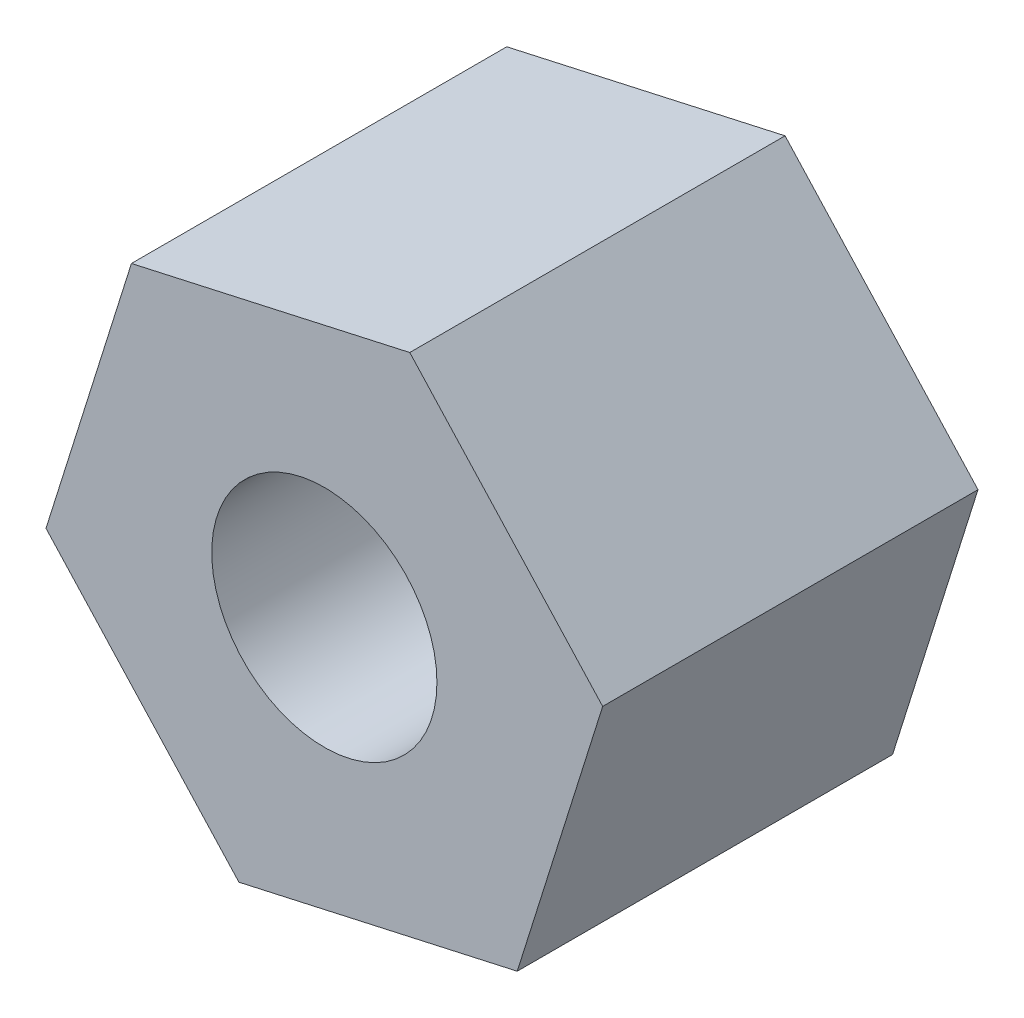
SolidWorks part; units mm, degrees
ref_plane "Front Plane" through (0, 0, 0) normal (0, 0, 1) x (1, 0, 0)
ref_plane "Top Plane" through (0, 0, 0) normal (0, 1, 0) x (1, 0, 0)
ref_plane "Right Plane" through (0, 0, 0) normal (1, 0, 0) x (0, 0, -1)
sketch "Sketch1" plane through (0, 0, 0) normal (0, 0, 1) x (1, 0, 0)
  line L1 (1.1381, 3.6245) -> (-2.5699, 2.7978)
  line L2 (-2.5699, 2.7978) -> (-3.7079, -0.8267)
  line L3 (-3.7079, -0.8267) -> (-1.1381, -3.6245)
  line L4 (-1.1381, -3.6245) -> (2.5699, -2.7978)
  line L5 (2.5699, -2.7978) -> (3.7079, 0.8267)
  line L6 (3.7079, 0.8267) -> (1.1381, 3.6245)
  circle A0 centre (0, 0) radius 3.29 construction
  circle A1 centre (0, 0) radius 1.5
  dimension "D2" = 3
  dimension "D1" = 6.58
extrude "Boss-Extrude1" add sketch "Sketch1" along normal blind 5
